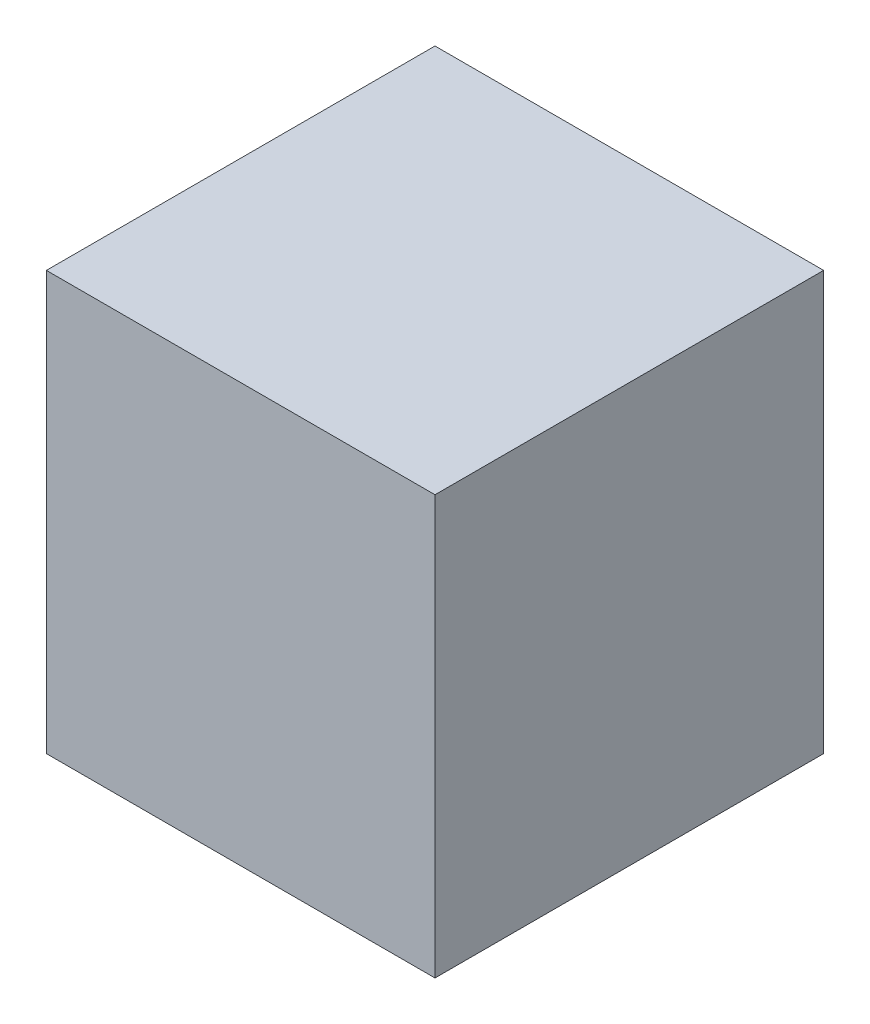
SolidWorks part; units mm, degrees
ref_plane "Front Plane" through (0, 0, 0) normal (0, 0, 1) x (1, 0, 0)
ref_plane "Top Plane" through (0, 0, 0) normal (0, 1, 0) x (1, 0, 0)
ref_plane "Right Plane" through (0, 0, 0) normal (1, 0, 0) x (0, 0, -1)
sketch "Sketch1" plane through (0, 0, 0) normal (0, 1, 0) x (1, 0, 0)
  line L1 (0, 0) -> (165.1, 0)
  line L2 (0, 0) -> (0, -165.1)
  line L3 (0, -165.1) -> (165.1, -165.1)
  line L4 (165.1, 0) -> (165.1, -165.1)
  dimension "D1" = 165.1
  dimension "D2" = 165.1
extrude "Boss-Extrude1" add sketch "Sketch1" along normal blind 177.8
sketch "Sketch2" plane through (0, 0, 165.1) normal (0, 0, 1) x (1, 0, 0)
  line L0 (82.55, 177.8) -> (82.55, 0) construction
  line L1 (0, 177.8) -> (165.1, 177.8) construction
  line L2 (0, 0) -> (165.1, 0) construction
  point P7 (82.55, 0)
